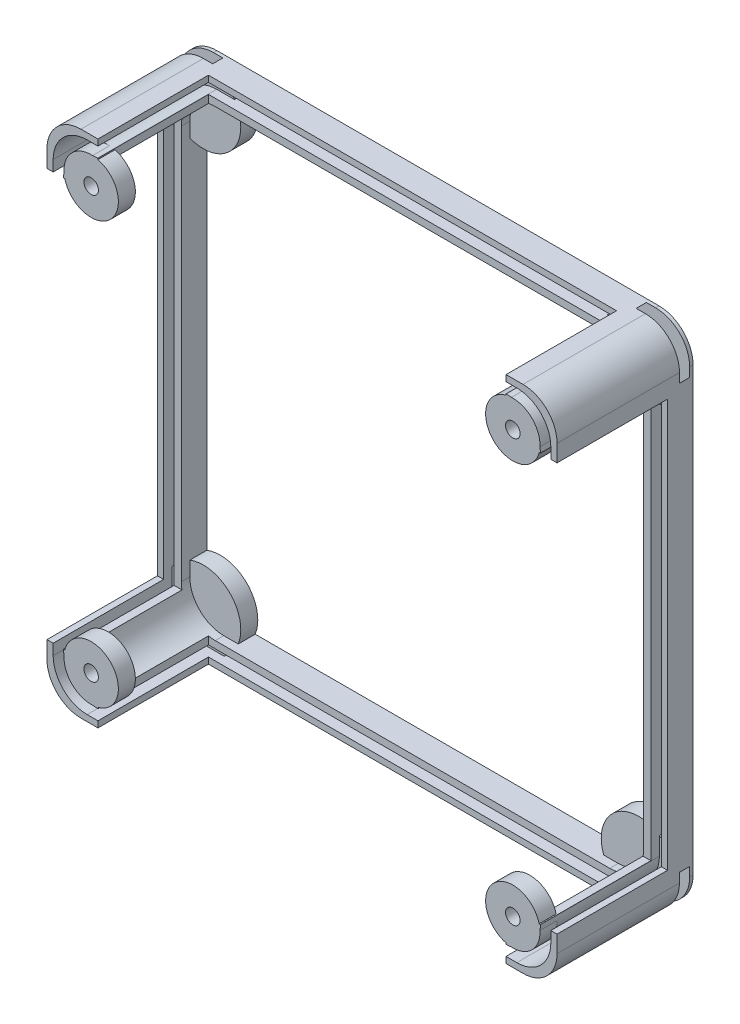
SolidWorks part; units mm, degrees
ref_plane "Front Plane" through (0, 0, 0) normal (0, 0, 1) x (1, 0, 0)
ref_plane "Top Plane" through (0, 0, 0) normal (0, 1, 0) x (1, 0, 0)
ref_plane "Right Plane" through (0, 0, 0) normal (1, 0, 0) x (0, 0, -1)
sketch "Sketch1" plane through (0, 0, 0) normal (0, 0, 1) x (1, 0, 0)
  circle A0 centre (-64, -64) radius 11
  circle A1 centre (-64, 64) radius 11
  circle A2 centre (64, -64) radius 11
  circle A3 centre (64, 64) radius 11
extrude "Boss-Extrude1" add sketch "Sketch1" along normal blind 5
sketch "Sketch2" plane through (0, 0, 0) normal (0, 0, 1) x (1, 0, 0)
  line L0 (-64, -64) -> (-84.1564, -84.1564) construction
  line L2 (-57.636, -70.364) -> (-77.7924, -90.5204)
  line L6 (-64, 64) -> (-81.1916, 81.1916) construction
  line L9 (-70.364, -57.636) -> (-90.5204, -77.7924)
  line L12 (-70.364, 57.636) -> (-87.5556, 74.8277)
  line L13 (-57.636, 70.364) -> (-74.8277, 87.5556)
  line L14 (64, -64) -> (80.8966, -80.8966) construction
  line L15 (70.364, -57.636) -> (87.2605, -74.5326)
  line L16 (57.636, -70.364) -> (74.5326, -87.2605)
  line L17 (64, 64) -> (83.0973, 83.0973) construction
  line L18 (57.636, 70.364) -> (76.7333, 89.4612)
  line L19 (70.364, 57.636) -> (89.4612, 76.7333)
  arc A13 (-70.364, 57.636) -> (-57.636, 70.364) centre (-64, 64) ccw
  arc A14 (-74.8277, 87.5556) -> (-87.5556, 74.8277) centre (-81.1916, 81.1916) ccw
  arc A15 (-57.636, -70.364) -> (-70.364, -57.636) centre (-64, -64) ccw
  arc A16 (-90.5204, -77.7924) -> (-77.7924, -90.5204) centre (-84.1564, -84.1564) ccw
  arc A17 (70.364, -57.636) -> (57.636, -70.364) centre (64, -64) ccw
  arc A18 (74.5326, -87.2605) -> (87.2605, -74.5326) centre (80.8966, -80.8966) ccw
  arc A19 (57.636, 70.364) -> (70.364, 57.636) centre (64, 64) ccw
  arc A20 (89.4612, 76.7333) -> (76.7333, 89.4612) centre (83.0973, 83.0973) ccw
  point P2 (-72.5958, 72.5958)
  point P3 (-74.0782, -74.0782)
  point P12 (72.4483, -72.4483)
  point P19 (73.5486, 73.5486)
extrude "Boss-Extrude2" add sketch "Sketch2" along normal blind 3 from offset 1 separate body
sketch "Sketch3" plane through (0, 0, 0) normal (0, 0, 1) x (1, 0, 0)
  line L1 (-75, -75) -> (75, -75)
  line L2 (-75, -75) -> (-75, 75)
  line L3 (-75, 75) -> (75, 75)
  line L4 (75, -75) -> (75, 75)
  line L5 (-75, -75) -> (75, 75) construction
  line L6 (-75, 75) -> (75, -75) construction
  line L7 (73.1762, 73.1762) -> (-73.1762, 73.1762)
  line L8 (73.1762, 73.1762) -> (73.1762, -73.1762)
  line L9 (73.1762, -73.1762) -> (-73.1762, -73.1762)
  line L10 (-73.1762, 73.1762) -> (-73.1762, -73.1762)
  line L11 (73.1762, 73.1762) -> (-73.1762, -73.1762) construction
  line L12 (73.1762, -73.1762) -> (-73.1762, 73.1762) construction
  line L13 (70.0994, 70.0994) -> (-70.0994, 70.0994)
  line L14 (70.0994, 70.0994) -> (70.0994, -70.0994)
  line L15 (70.0994, -70.0994) -> (-70.0994, -70.0994)
  line L16 (-70.0994, 70.0994) -> (-70.0994, -70.0994)
  line L17 (70.0994, 70.0994) -> (-70.0994, -70.0994) construction
  line L18 (70.0994, -70.0994) -> (-70.0994, 70.0994) construction
  line L19 (68, 68) -> (-68, 68)
  line L20 (68, 68) -> (68, -68)
  line L21 (68, -68) -> (-68, -68)
  line L22 (-68, 68) -> (-68, -68)
  line L23 (68, 68) -> (-68, -68) construction
  line L24 (68, -68) -> (-68, 68) construction
  point P0 (0, 0)
  point P5 (0, 0)
  point P11 (0, 0)
  point P13 (0, 0)
extrude "Boss-Extrude4" add sketch "Sketch3" along normal blind 40 separate body contours L1 L4 L3 L2 L10 L7 L8 L9 | L13 L16 L15 L14 L22 L19 L20 L21
fillet "Fillet1" radius 10 8 edges at (73.1762, -73.1762, 20) (75, -75, 20) (73.1762, 73.1762, 20) (75, 75, 20) (-73.1762, 73.1762, 20) (-75, 75, 20) (-73.1762, -73.1762, 20) (-75, -75, 20)
fillet "Fillet2" radius 10 8 edges at (70.0994, 70.0994, 20) (68, 68, 20) (70.0994, -70.0994, 20) (68, -68, 20) (-70.0994, -70.0994, 20) (-68, -68, 20) (-68, 68, 20) (-70.0994, 70.0994, 20)
sketch "Sketch6" plane through (0, 0, 0) normal (0, 0, 1) x (1, 0, 0)
  line L1 (80.2178, -60) -> (-80.2178, -60)
  line L2 (80.2178, -60) -> (80.2178, 60)
  line L3 (80.2178, 60) -> (-80.2178, 60)
  line L4 (-80.2178, -60) -> (-80.2178, 60)
  line L5 (80.2178, -60) -> (-80.2178, 60) construction
  line L6 (80.2178, 60) -> (-80.2178, -60) construction
  line L7 (60, -83.8886) -> (-60, -83.8886)
  line L8 (60, -83.8886) -> (60, 83.8886)
  line L9 (60, 83.8886) -> (-60, 83.8886)
  line L10 (-60, -83.8886) -> (-60, 83.8886)
  line L11 (60, -83.8886) -> (-60, 83.8886) construction
  line L12 (60, 83.8886) -> (-60, -83.8886) construction
  point P0 (0, 0)
  point P6 (0, 0)
combine bodies "Combine4" operation type add bodies to combine 101 104 103 102 124 125
combine bodies "Combine8" operation type subtract main body 130 bodies to subtract 113 121 122 123
extrude "Boss-Extrude6" add sketch "Sketch6" against normal blind 32.5 from surface at 40 separate body contours L10 L1 L8 L3 | L10 L7 L8 L1 | L1 L10 L3 L4 | L10 L3 L8 L9 | L8 L1 L2 L3 starting at face at (0, 0, 40)
combine bodies "Combine9" operation type subtract main body 132 bodies to subtract 133
ref_plane "Plane1" through (0, 0, 40) normal (0, 0, 1) x (1, 0, 0)
sketch "Sketch7" plane through (0, 0, 40) normal (0, 0, 1) x (1, 0, 0)
  circle A0 centre (-62, -62) radius 8
  circle A1 centre (-62, 62) radius 8
  circle A2 centre (62, -62) radius 8
  circle A3 centre (62, 62) radius 8
  circle A4 centre (-62, 62) radius 2.14
  circle A5 centre (-62, -62) radius 2.14
  circle A6 centre (62, 62) radius 2.14
  circle A7 centre (62, -62) radius 2.14
extrude "Boss-Extrude7" add sketch "Sketch7" against normal blind 5
